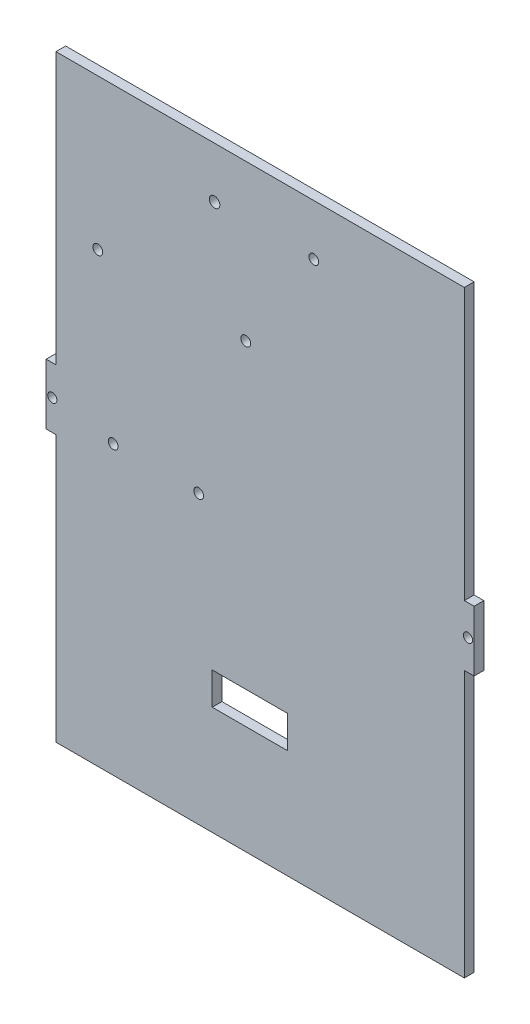
SolidWorks part; units mm, degrees
ref_plane "Front Plane" through (0, 0, 0) normal (0, 0, 1) x (1, 0, 0)
ref_plane "Top Plane" through (0, 0, 0) normal (0, 1, 0) x (1, 0, 0)
ref_plane "Right Plane" through (0, 0, 0) normal (1, 0, 0) x (0, 0, -1)
sketch "Sketch1" plane through (0, 0, 0) normal (0, 0, 1) x (1, 0, 0)
  line L1 (-69.85, 100.01) -> (69.85, 100.01)
  line L2 (-69.85, 100.01) -> (-69.85, -100.01)
  line L3 (-69.85, -100.01) -> (69.85, -100.01)
  line L4 (69.85, 100.01) -> (69.85, -100.01)
  line L5 (-69.85, 100.01) -> (69.85, -100.01) construction
  line L6 (-69.85, -100.01) -> (69.85, 100.01) construction
  point P0 (0, 0)
  dimension "D1" = 200.02
  dimension "D2" = 139.7
extrude "Boss-Extrude1" add sketch "Sketch1" along normal blind 3.18
sketch "Sketch2" plane through (0, 0, 3.18) normal (0, 0, 1) x (1, 0, 0)
  line L0 (0, 0) -> (69.85, 0) construction
  line L1 (-10, 100.01) -> (10, 100.01)
  line L2 (-10, 100.01) -> (-10, 96.83)
  line L3 (-10, 96.83) -> (-1.5, 96.83)
  line L4 (10, 100.01) -> (10, 96.83)
  line L5 (69.85, -100.01) -> (69.85, 100.01) construction
  line L6 (0, 0) -> (0, 100.01) construction
  line L7 (-1.5, 86.83) -> (1.5, 86.83)
  line L8 (-1.5, 86.83) -> (-1.5, 89.83)
  line L10 (1.5, 86.83) -> (1.5, 89.83)
  line L12 (69.85, 100.01) -> (-69.85, 100.01) construction
  line L13 (3.5, 92.83) -> (1.5, 92.83)
  line L14 (3.5, 92.83) -> (3.5, 89.83)
  line L15 (3.5, 89.83) -> (1.5, 89.83)
  line L16 (-3.5, 92.83) -> (-3.5, 89.83)
  line L17 (-10, -100.01) -> (-10, -96.83)
  line L18 (-10, -96.83) -> (-1.5, -96.83)
  line L19 (-1.5, -92.83) -> (-1.5, -96.83)
  line L20 (-1.5, -92.83) -> (-3.5, -92.83)
  line L21 (-3.5, -92.83) -> (-3.5, -89.83)
  line L22 (1.5, 96.83) -> (10, 96.83)
  line L23 (-1.5, 92.83) -> (-3.5, 92.83)
  line L24 (-1.5, -89.83) -> (-3.5, -89.83)
  line L25 (-1.5, -86.83) -> (-1.5, -89.83)
  line L26 (-1.5, -86.83) -> (1.5, -86.83)
  line L27 (-1.5, 89.83) -> (-3.5, 89.83)
  line L28 (1.5, -86.83) -> (1.5, -89.83)
  line L29 (-1.5, 92.83) -> (-1.5, 96.83)
  line L30 (1.5, 92.83) -> (1.5, 96.83)
  line L31 (3.5, -89.83) -> (1.5, -89.83)
  line L32 (3.5, -92.83) -> (3.5, -89.83)
  line L33 (3.5, -92.83) -> (1.5, -92.83)
  line L34 (1.5, -92.83) -> (1.5, -96.83)
  line L35 (1.5, -96.83) -> (10, -96.83)
  line L36 (10, -100.01) -> (10, -96.83)
  line L37 (-10, -100.01) -> (10, -100.01)
  line L38 (-69.85, 100.01) -> (-69.85, -100.01) construction
  line L39 (-69.85, 100.01) -> (-66.67, 100.01)
  line L40 (-69.85, 100.01) -> (-69.85, 9.875)
  line L41 (-69.85, 9.875) -> (-66.67, 9.875)
  line L42 (-66.67, 100.01) -> (-66.67, 9.875)
  line L43 (-69.85, -100.01) -> (-66.67, -100.01)
  line L44 (-69.85, -100.01) -> (-69.85, -9.875)
  line L45 (-69.85, -9.875) -> (-66.67, -9.875)
  line L46 (-66.67, -100.01) -> (-66.67, -9.875)
  line L47 (69.85, -9.875) -> (66.67, -9.875)
  line L48 (66.67, -100.01) -> (66.67, -9.875)
  line L49 (69.85, -100.01) -> (66.67, -100.01)
  line L50 (69.85, -100.01) -> (69.85, -9.875)
  line L51 (69.85, 9.875) -> (66.67, 9.875)
  line L52 (66.67, 100.01) -> (66.67, 9.875)
  line L53 (69.85, 100.01) -> (66.67, 100.01)
  line L54 (69.85, 100.01) -> (69.85, 9.875)
  circle A0 centre (-67.85, 0) radius 1.5
  circle A1 centre (67.85, 0) radius 1.5
  point P0 (0, 50.5662)
  point P5 (0, 32.0079)
  point P10 (15.4931, 34.4893)
  dimension "D11" = 3
  dimension "D12" = 2
  dimension "D1" = 20
  dimension "D2" = 19.75
  dimension "D3" = 4
  dimension "D4" = 3
  dimension "D5" = 3.18
  dimension "D6" = 7
  dimension "D7" = 3
  dimension "D8" = 3
  dimension "D9" = 3.18
  dimension "D10" = 3.18
extrude "Cut-Extrude1" cut sketch "Sketch2" against normal through all
sketch "Sketch5" plane through (0, 0, 3.18) normal (0, 0, 1) x (1, 0, 0)
  line L1 (-44.4479, 84.2814) -> (44.4479, 84.2814)
  line L2 (-44.4479, 84.2814) -> (-44.4479, -84.2814)
  line L3 (-44.4479, -84.2814) -> (44.4479, -84.2814)
  line L4 (44.4479, 84.2814) -> (44.4479, -84.2814)
  line L5 (-44.4479, 84.2814) -> (44.4479, -84.2814) construction
  line L6 (-44.4479, -84.2814) -> (44.4479, 84.2814) construction
  point P0 (0, 0)
extrude "Boss-Extrude2" add sketch "Sketch5" against normal blind 3.18
sketch "Sketch6" plane through (0, 0, 3.18) normal (0, 0, 1) x (1, 0, 0)
  line L1 (-10, 100.01) -> (10, 100.01)
  line L2 (-10, 100.01) -> (-10, -100.01)
  line L3 (-10, -100.01) -> (10, -100.01)
  line L4 (10, 100.01) -> (10, -100.01)
extrude "Boss-Extrude3" add sketch "Sketch6" against normal blind 3.18
sketch "Sketch7" plane through (0, 0, 3.18) normal (0, 0, 1) x (1, 0, 0)
  line L0 (0, 0) -> (0, -20.0062) construction
  line L1 (-66.67, -100.01) -> (-9.875, -100.01)
  line L2 (-66.67, -100.01) -> (-66.67, -96.83)
  line L3 (-66.67, -96.83) -> (-9.875, -96.83)
  line L4 (-9.875, -100.01) -> (-9.875, -96.83)
  line L5 (66.67, -100.01) -> (9.875, -100.01)
  line L6 (66.67, -100.01) -> (66.67, -96.83)
  line L7 (66.67, -96.83) -> (9.875, -96.83)
  line L8 (9.875, -100.01) -> (9.875, -96.83)
  dimension "D1" = 3.18
  dimension "D2" = 3.18
  dimension "D3" = 19.75
extrude "Cut-Extrude4" cut sketch "Sketch7" against normal through all
sketch "Sketch8" plane through (0, 0, 3.18) normal (0, 0, 1) x (1, 0, 0)
  line L0 (-66.67, 9.875) -> (-66.67, 100.01) construction
  line L1 (66.67, 100.01) -> (-66.67, 100.01)
  line L2 (66.67, 100.01) -> (66.67, 98.42)
  line L3 (66.67, 98.42) -> (-66.67, 98.42)
  line L4 (-66.67, 100.01) -> (-66.67, 98.42)
  line L5 (-9.875, 98.42) -> (-69.85, 98.42) construction
extrude "Cut-Extrude5" cut sketch "Sketch8" against normal through all
sketch "Sketch9" plane through (0, 0, 3.18) normal (0, 0, 1) x (1, 0, 0)
  circle A0 centre (-52.9813, 49.2929) radius 1.6
  circle A1 centre (-4.6839, 47.6157) radius 1.6
  circle A3 centre (-20.065, -3.1598) radius 1.6
  circle A4 centre (-47.9649, -3.1152) radius 1.6
  dimension "D1" = 3.2
  dimension "D2" = 3.2
  dimension "D3" = 3.2
  dimension "D4" = 3.2
  dimension "D5" = 52.4081
  dimension "D6" = 27.9
  dimension "D7" = 48.2974
  dimension "D8" = 50.7755
  dimension "D9" = 61.9254
  dimension "D10" = 66.6849
extrude "Cut-Extrude6" cut sketch "Sketch9" against normal through all
sketch "Sketch10" plane through (0, 0, 3.18) normal (0, 0, 1) x (1, 0, 0)
  line L1 (8.9231, -61.4181) -> (-15.6427, -61.4181)
  line L2 (8.9231, -61.4181) -> (8.9231, -50.8809)
  line L3 (8.9231, -50.8809) -> (-15.6427, -50.8809)
  line L4 (-15.6427, -61.4181) -> (-15.6427, -50.8809)
extrude "Cut-Extrude7" cut sketch "Sketch10" against normal blind 3.18
sketch "Sketch11" plane through (0, 0, 3.18) normal (0, 0, 1) x (1, 0, 0)
  circle A0 centre (17.5239, 81.7974) radius 1.59
  circle A1 centre (-14.8831, 81.7974) radius 1.7179
extrude "Cut-Extrude8" cut sketch "Sketch11" against normal blind 35
sketch "Sketch12" plane through (-9.875, 0, 0) normal (-1, 0, 0) x (0, 0, 1)
  line L1 (3.18, -96.83) -> (0, -96.83)
  line L2 (3.18, -96.83) -> (3.18, -100.01)
  line L3 (3.18, -100.01) -> (0, -100.01)
  line L4 (0, -96.83) -> (0, -100.01)
extrude "Cut-Extrude9" cut sketch "Sketch12" against normal through all
